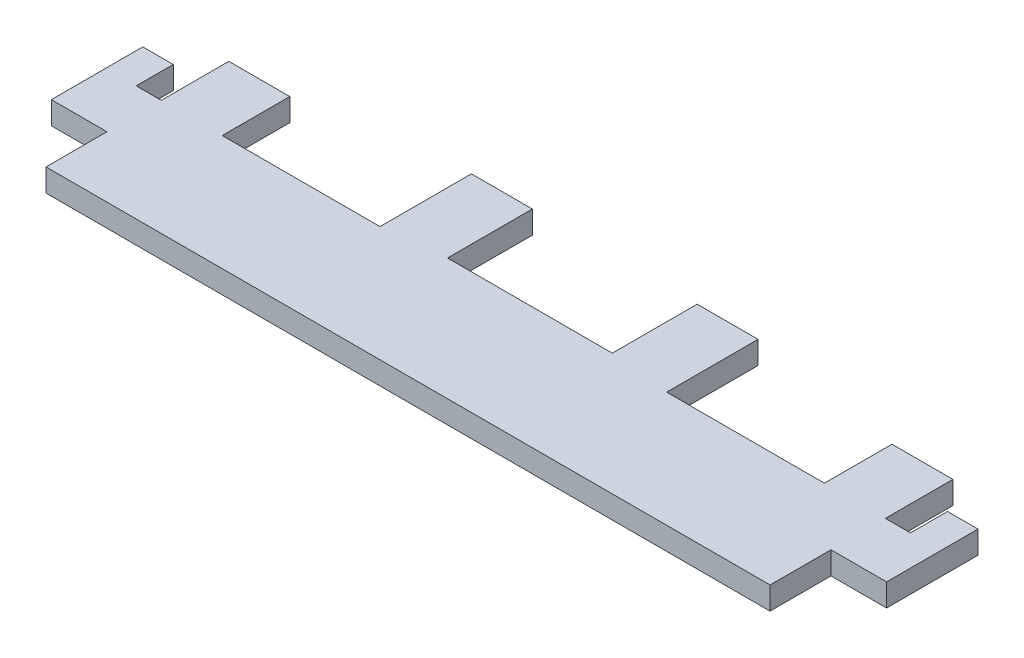
SolidWorks part; units mm, degrees
ref_plane "Front Plane" through (0, 0, 0) normal (0, 0, 1) x (1, 0, 0)
ref_plane "Top Plane" through (0, 0, 0) normal (0, 1, 0) x (1, 0, 0)
ref_plane "Right Plane" through (0, 0, 0) normal (1, 0, 0) x (0, 0, -1)
sketch "Sketch1" plane through (0, 0, 0) normal (0, 1, 0) x (1, 0, 0)
  line L0 (5.7912, 6.35) -> (5.7912, 19.05)
  line L1 (5.7912, 19.05) -> (2.6162, 19.05)
  line L2 (2.6162, 19.05) -> (2.6162, 12.0142)
  line L3 (-22.7838, 12.0142) -> (-6.35, 12.0142)
  line L4 (-22.7838, 12.0142) -> (-22.7838, 21.5392)
  line L5 (-22.7838, 21.5392) -> (-29.1338, 21.5392)
  line L6 (-29.1338, 21.5392) -> (-29.1338, 12.7)
  line L7 (-29.1338, 12.7) -> (-46.3042, 12.7)
  line L8 (0, 0) -> (-75.438, 0)
  line L9 (-37.719, 0) -> (-37.719, 12.7) construction
  line L10 (5.7912, 6.35) -> (0, 6.35)
  line L11 (0, 6.35) -> (0, 0)
  line L12 (-75.438, 12.0142) -> (-78.0542, 12.0142)
  line L13 (-75.438, 19.05) -> (-75.438, 12.0142)
  line L14 (-69.088, 19.05) -> (-75.438, 19.05)
  line L15 (-69.088, 12.0142) -> (-69.088, 19.05)
  line L16 (-75.438, 6.35) -> (-75.438, 0)
  line L17 (-6.35, 12.0142) -> (-6.35, 19.05)
  line L18 (-6.35, 19.05) -> (0, 19.05)
  line L19 (0, 19.05) -> (0, 12.0142)
  line L20 (0, 12.0142) -> (2.6162, 12.0142)
  line L21 (-81.2292, 6.35) -> (-75.438, 6.35)
  line L22 (-46.3042, 21.5392) -> (-46.3042, 12.7)
  line L23 (-52.6542, 21.5392) -> (-46.3042, 21.5392)
  line L24 (-52.6542, 12.0142) -> (-52.6542, 21.5392)
  line L25 (-52.6542, 12.0142) -> (-69.088, 12.0142)
  line L26 (-78.0542, 19.05) -> (-78.0542, 12.0142)
  line L27 (-81.2292, 19.05) -> (-78.0542, 19.05)
  line L28 (-81.2292, 6.35) -> (-81.2292, 19.05)
  dimension "D1" = 8.8392
  dimension "D2" = 7.0358
  dimension "D3" = 6.35
  dimension "D4" = 3.175
  dimension "D5" = 19.05
  dimension "D6" = 25.4
  dimension "D7" = 8.5852
  dimension "D8" = 6.35
  dimension "D9" = 2.6162
  dimension "D10" = 12.7
  dimension "D11" = 6.35
extrude "Boss-Extrude1" add sketch "Sketch1" along normal blind 2.3622
sketch "Sketch2" plane through (0, 2.3622, 0) normal (0, 1, 0) x (1, 0, 0)
  line L0 (2.6162, 19.05) -> (2.6162, 12.0142) construction
  line L1 (5.7912, 19.05) -> (2.6162, 19.05)
  line L2 (5.7912, 19.05) -> (5.7912, 15.875)
  line L3 (5.7912, 15.875) -> (2.6162, 15.875)
  line L4 (2.6162, 19.05) -> (2.6162, 15.875)
  line L5 (-81.2292, 6.35) -> (-75.438, 6.35) construction
  line L6 (-81.2292, 19.05) -> (-78.0542, 19.05)
  line L7 (-81.2292, 19.05) -> (-81.2292, 15.875)
  line L8 (-81.2292, 15.875) -> (-78.0542, 15.875)
  line L9 (-78.0542, 19.05) -> (-78.0542, 15.875)
  line L10 (0, 6.35) -> (5.7912, 6.35) construction
  line L11 (-78.0542, 12.0142) -> (-78.0542, 19.05) construction
  dimension "D1" = 9.525
  dimension "D2" = 9.525
extrude "Cut-Extrude1" cut sketch "Sketch2" against normal blind 2.54
